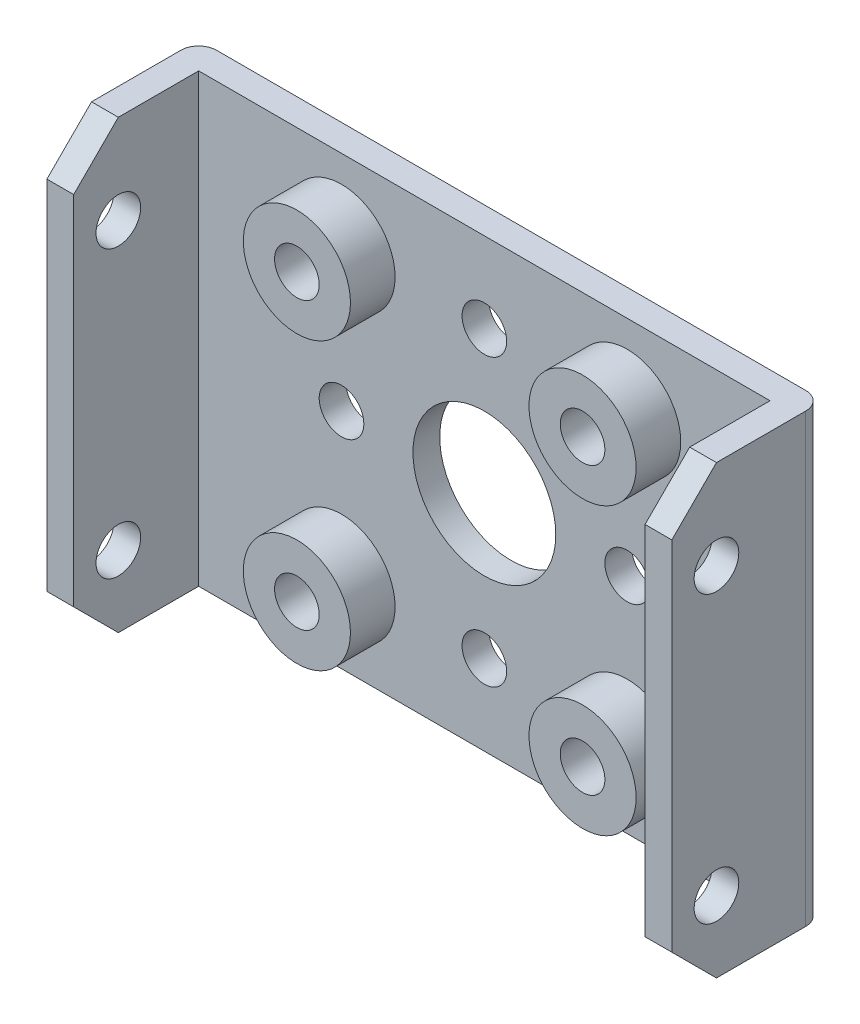
SolidWorks part; units mm, degrees
ref_plane "Front Plane" through (0, 0, 0) normal (0, 0, 1) x (1, 0, 0)
ref_plane "Top Plane" through (0, 0, 0) normal (0, 1, 0) x (1, 0, 0)
ref_plane "Right Plane" through (0, 0, 0) normal (1, 0, 0) x (0, 0, -1)
sketch "Sketch1" plane through (0, 0, 0) normal (0, 0, 1) x (1, 0, 0)
  line L1 (35, 0) -> (0, 0)
  line L2 (35, 0) -> (35, 25)
  line L3 (35, 25) -> (0, 25)
  line L4 (0, 0) -> (0, 25)
  point P6 (17.5, 0)
  dimension "D1" = 35
  dimension "D2" = 25
  dimension "D3" = 0
  dimension "D4" = 0
extrude "Boss-Extrude1" add sketch "Sketch1" along normal blind 8.5
sketch "Sketch3" plane through (0, 0, 8.5) normal (0, 0, 1) x (1, 0, 0)
  line L0 (35, 25) -> (0, 25) construction
  line L1 (1.5, 25) -> (33.5, 25)
  line L2 (1.5, 25) -> (1.5, 0)
  line L3 (1.5, 0) -> (33.5, 0)
  line L4 (33.5, 25) -> (33.5, 0)
  line L5 (0, 25) -> (0, 0) construction
  line L6 (35, 0) -> (35, 25) construction
  point P6 (1.5, 12.5)
  point P11 (33.5, 12.5)
  dimension "D1" = 1.5
  dimension "D2" = 25
  dimension "D3" = 1.5
extrude "Cut-Extrude1" cut sketch "Sketch3" against normal blind 7
fillet "Fillet1" radius 1 2 edges at (35, 12.5, 0) (0, 12.5, 0)
chamfer "Chamfer1" distance 2.5 4 edges at (34.25, 0, 8.5) (0.75, 0, 8.5) (34.25, 25, 8.5) (0.75, 25, 8.5)
sketch "Sketch4" plane through (0, 0, 0) normal (-1, 0, 0) x (0, 0, 1)
  line L0 (6, 25) -> (1, 25) construction
  line L1 (8.5, 22.5) -> (8.5, 2.5) construction
  circle A0 centre (6, 20) radius 1.25
  circle A1 centre (6, 4) radius 1.25
  dimension "D1" = 2.5
  dimension "D2" = 5
  dimension "D3" = 2.5
  dimension "D5" = 16
  dimension "D4" = 2
extrude "Cut-Extrude2" cut sketch "Sketch4" against normal blind 35
sketch "Sketch5" plane through (0, 0, 1.5) normal (0, 0, 1) x (1, 0, 0)
  line L0 (1.5, 25) -> (1.5, 0) construction
  line L1 (1.5, 0) -> (33.5, 0) construction
  circle A9 centre (9.5, 4.5) radius 3
  circle A10 centre (25.5, 4.5) radius 3
  circle A11 centre (25.5, 20.5) radius 3
  circle A12 centre (9.5, 20.5) radius 3
  dimension "D1" = 6
  dimension "D6" = 16
  dimension "D4" = 2
  dimension "D9" = 32
  dimension "D8" = 8
  dimension "D2" = 8
  dimension "D3" = 4.5
  dimension "D7" = 16
  dimension "D5" = 2
extrude "Boss-Extrude3" add sketch "Sketch5" along normal blind 2.5
sketch "Sketch7" plane through (0, 0, 1.5) normal (0, 0, 1) x (1, 0, 0)
  line L1 (1, 0) -> (34, 0) construction
  line L3 (1.5, 25) -> (1.5, 0) construction
  circle A3 centre (17.5, 12.5) radius 4
  circle A8 centre (9.5, 4.5) radius 1.25
  circle A9 centre (17.5, 4.5) radius 1.25
  circle A10 centre (25.5, 4.5) radius 1.25
  circle A11 centre (17.5, 12.5) radius 1.25 [skipped]
  circle A12 centre (25.5, 12.5) radius 1.25
  circle A13 centre (17.5, 20.5) radius 1.25
  circle A14 centre (25.5, 20.5) radius 1.25
  circle A15 centre (9.5, 12.5) radius 1.25
  circle A16 centre (9.5, 20.5) radius 1.25
  circle A17 centre (9.5, 4.5) radius 3 construction
  dimension "D2" = 2.5
  dimension "D7" = 8
  dimension "D4" = 3
  dimension "D5" = 3
  dimension "D3" = 8
  dimension "D6" = 8
  dimension "D17" = 4.5
extrude "Cut-Extrude3" cut sketch "Sketch7" against normal blind 1.5 and the other way blind 2.5
